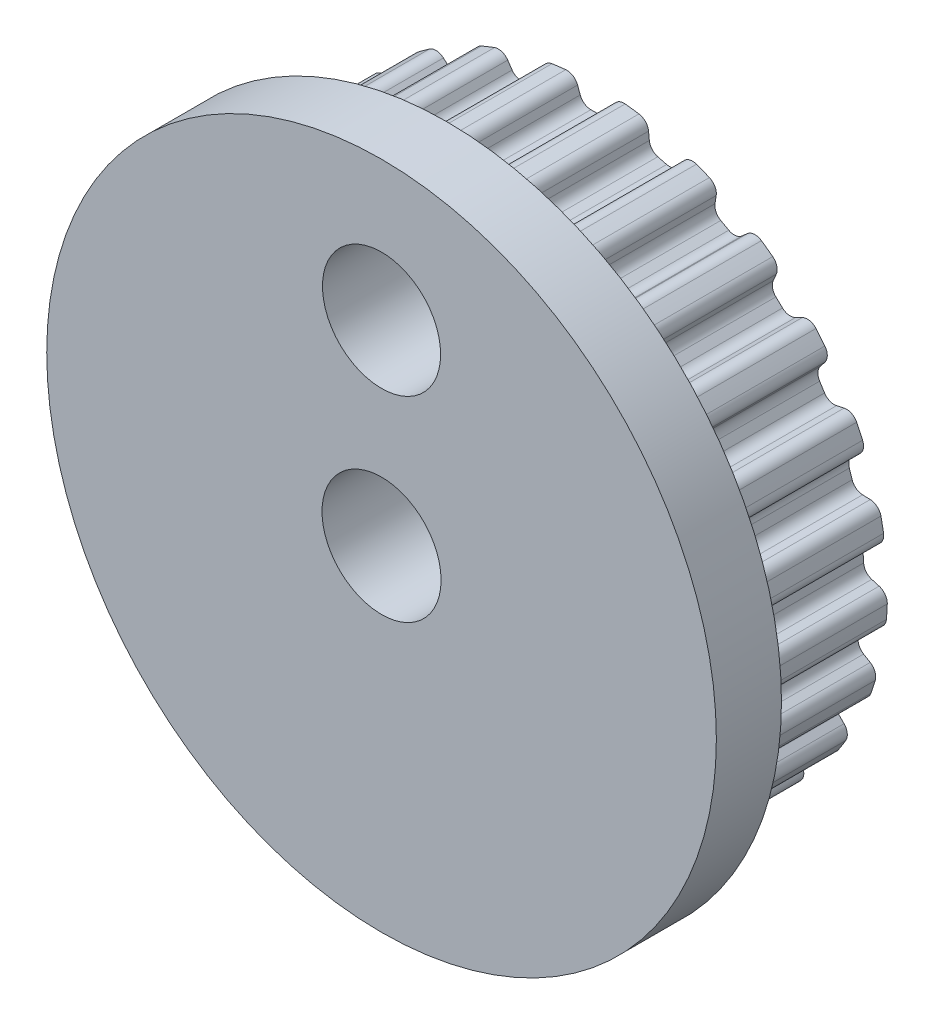
SolidWorks part; units mm, degrees
ref_plane "Front Plane" through (0, 0, 0) normal (0, 0, 1) x (1, 0, 0)
ref_plane "Top Plane" through (0, 0, 0) normal (0, 1, 0) x (1, 0, 0)
ref_plane "Right Plane" through (0, 0, 0) normal (1, 0, 0) x (0, 0, -1)
ref_plane "Plane1" through (0, 0, -5.3) normal (0, 0, -1) x (-1, 0, 0)
sketch "Sketch1" plane through (0, 0, -5.3) normal (0, 0, -1) x (-1, 0, 0)
  line L0 (-2.7705, -6.663) -> (-2.5415, -6.7537)
  line L1 (-2.3491, -7.0456) -> (-2.3549, -7.2528)
  line L2 (-1.4305, -7.4901) -> (-1.3357, -7.3057)
  line L3 (-1.0264, -7.1427) -> (-0.7821, -7.1735)
  line L4 (-0.5231, -7.4084) -> (-0.4772, -7.6106)
  line L5 (0.4772, -7.6106) -> (0.5231, -7.4084)
  line L6 (0.7821, -7.1735) -> (1.0264, -7.1427)
  line L7 (1.3357, -7.3057) -> (1.4305, -7.4901)
  line L8 (2.3549, -7.2528) -> (2.3491, -7.0456)
  line L9 (2.5415, -6.7537) -> (2.7705, -6.663)
  line L10 (3.1106, -6.744) -> (3.2483, -6.8991)
  line L11 (4.0846, -6.4393) -> (4.0274, -6.24)
  line L12 (4.1413, -5.9094) -> (4.3405, -5.7647)
  line L13 (4.6901, -5.7586) -> (4.862, -5.8745)
  line L14 (5.5576, -5.2212) -> (5.4527, -5.0424)
  line L15 (5.4808, -4.6939) -> (5.6377, -4.5041)
  line L16 (5.9748, -4.4113) -> (6.1701, -4.4808)
  line L17 (6.6815, -3.6751) -> (6.5354, -3.528)
  line L18 (6.4759, -3.1834) -> (6.5808, -2.9606)
  line L19 (6.8842, -2.7868) -> (7.0906, -2.8056)
  line L20 (7.3855, -1.898) -> (7.2075, -1.7918)
  line L21 (7.0641, -1.4729) -> (7.1103, -1.231)
  line L22 (7.3609, -0.9872) -> (7.5656, -0.9541)
  line L23 (7.6255, -0.0016) -> (7.4266, 0.0569)
  line L24 (7.2085, 0.3301) -> (7.193, 0.5759)
  line L25 (7.3752, 0.8744) -> (7.5652, 0.9574)
  line L26 (7.3864, 1.8948) -> (7.1792, 1.902)
  line L27 (6.8999, 2.1125) -> (6.8238, 2.3467)
  line L28 (6.9261, 2.681) -> (7.0894, 2.8087)
  line L29 (6.6831, 3.6722) -> (6.4806, 3.6277)
  line L30 (6.1578, 3.762) -> (6.0259, 3.9699)
  line L31 (6.0417, 4.3192) -> (6.1682, 4.4835)
  line L32 (5.5599, 5.2188) -> (5.3748, 5.1254)
  line L33 (5.0288, 5.1752) -> (4.8493, 5.3438)
  line L34 (4.7777, 5.6861) -> (4.8594, 5.8766)
  line L35 (4.0874, 6.4376) -> (3.9314, 6.301)
  line L36 (3.5837, 6.2632) -> (3.368, 6.3819)
  line L37 (3.2136, 6.6956) -> (3.2453, 6.9005)
  line L38 (2.358, 7.2518) -> (2.2409, 7.0807)
  line L39 (1.9136, 6.9577) -> (1.675, 7.0189)
  line L40 (1.4475, 7.2844) -> (1.4273, 7.4908)
  line L41 (0.4805, 7.6104) -> (0.4095, 7.4156)
  line L42 (0.1231, 7.215) -> (-0.1231, 7.215)
  line L43 (-0.4095, 7.4156) -> (-0.4805, 7.6104)
  line L44 (-1.4273, 7.4908) -> (-1.4475, 7.2844)
  line L45 (-1.675, 7.0189) -> (-1.9136, 6.9577)
  line L46 (-2.2409, 7.0807) -> (-2.358, 7.2518)
  line L47 (-3.2453, 6.9005) -> (-3.2136, 6.6956)
  line L48 (-3.368, 6.3819) -> (-3.5837, 6.2632)
  line L49 (-3.9314, 6.301) -> (-4.0874, 6.4376)
  line L50 (-4.8594, 5.8766) -> (-4.7777, 5.6861)
  line L51 (-4.8493, 5.3438) -> (-5.0288, 5.1752)
  line L52 (-5.3748, 5.1254) -> (-5.5599, 5.2188)
  line L53 (-6.1682, 4.4835) -> (-6.0417, 4.3192)
  line L54 (-6.0259, 3.9699) -> (-6.1578, 3.762)
  line L55 (-6.4806, 3.6277) -> (-6.6831, 3.6722)
  line L56 (-7.0894, 2.8087) -> (-6.9261, 2.681)
  line L57 (-6.8238, 2.3467) -> (-6.8999, 2.1125)
  line L58 (-7.1792, 1.902) -> (-7.3864, 1.8948)
  line L59 (-7.5652, 0.9574) -> (-7.3752, 0.8744)
  line L60 (-7.193, 0.5759) -> (-7.2085, 0.3301)
  line L61 (-7.4266, 0.0569) -> (-7.6255, -0.0016)
  line L62 (-7.5656, -0.9541) -> (-7.3609, -0.9872)
  line L63 (-7.1103, -1.231) -> (-7.0641, -1.4729)
  line L64 (-7.2075, -1.7918) -> (-7.3855, -1.898)
  line L65 (-7.0906, -2.8056) -> (-6.8842, -2.7868)
  line L66 (-6.5808, -2.9606) -> (-6.4759, -3.1834)
  line L67 (-6.5354, -3.528) -> (-6.6815, -3.6751)
  line L68 (-6.1701, -4.4808) -> (-5.9748, -4.4113)
  line L69 (-5.6377, -4.5041) -> (-5.4808, -4.6939)
  line L70 (-5.4527, -5.0424) -> (-5.5576, -5.2212)
  line L71 (-4.862, -5.8745) -> (-4.6901, -5.7586)
  line L72 (-4.3405, -5.7647) -> (-4.1413, -5.9094)
  line L73 (-4.0274, -6.24) -> (-4.0846, -6.4393)
  line L74 (-3.2483, -6.8991) -> (-3.1106, -6.744)
  arc A2 (-2.5415, -6.7537) -> (-2.3491, -7.0456) centre (-2.6537, -7.0371) cw
  arc A3 (-2.3549, -7.2528) -> (-2.133, -7.5547) centre (-2.0502, -7.2613) ccw
  arc A4 (-2.133, -7.5547) -> (-1.7703, -7.6478) centre (0, 0) ccw
  arc A5 (-1.7703, -7.6478) -> (-1.4305, -7.4901) centre (-1.7016, -7.3508) ccw
  arc A6 (-1.3357, -7.3057) -> (-1.0264, -7.1427) centre (-1.0646, -7.4451) cw
  arc A7 (-0.7821, -7.1735) -> (-0.5231, -7.4084) centre (-0.8203, -7.4759) cw
  arc A8 (-0.4772, -7.6106) -> (-0.1872, -7.8478) centre (-0.1799, -7.5431) ccw
  arc A9 (-0.1872, -7.8478) -> (0.1872, -7.8478) centre (0, 0) ccw
  arc A10 (0.1872, -7.8478) -> (0.4772, -7.6106) centre (0.1799, -7.5431) ccw
  arc A11 (0.5231, -7.4084) -> (0.7821, -7.1735) centre (0.8203, -7.4759) cw
  arc A12 (1.0264, -7.1427) -> (1.3357, -7.3057) centre (1.0646, -7.4451) cw
  arc A13 (1.4305, -7.4901) -> (1.7703, -7.6478) centre (1.7016, -7.3508) ccw
  arc A14 (1.7703, -7.6478) -> (2.133, -7.5547) centre (0, 0) ccw
  arc A15 (2.133, -7.5547) -> (2.3549, -7.2528) centre (2.0502, -7.2613) ccw
  arc A16 (2.3491, -7.0456) -> (2.5415, -6.7537) centre (2.6537, -7.0371) cw
  arc A17 (2.7705, -6.663) -> (3.1106, -6.744) centre (2.8827, -6.9464) cw
  arc A18 (3.2483, -6.8991) -> (3.6166, -6.9672) centre (3.4762, -6.6967) ccw
  arc A19 (3.6166, -6.9672) -> (3.9447, -6.7869) centre (0, 0) ccw
  arc A20 (3.9447, -6.7869) -> (4.0846, -6.4393) centre (3.7916, -6.5233) ccw
  arc A21 (4.0274, -6.24) -> (4.1413, -5.9094) centre (4.3204, -6.156) cw
  arc A22 (4.3405, -5.7647) -> (4.6901, -5.7586) centre (4.5196, -6.0113) cw
  arc A23 (4.862, -5.8745) -> (5.2357, -5.8489) centre (5.0324, -5.6218) ccw
  arc A24 (5.2357, -5.8489) -> (5.5086, -5.5926) centre (0, 0) ccw
  arc A25 (5.5086, -5.5926) -> (5.5576, -5.2212) centre (5.2947, -5.3755) ccw
  arc A26 (5.4527, -5.0424) -> (5.4808, -4.6939) centre (5.7156, -4.8882) cw
  arc A27 (5.6377, -4.5041) -> (5.9748, -4.4113) centre (5.8726, -4.6984) cw
  arc A28 (6.1701, -4.4808) -> (6.5258, -4.3631) centre (6.2724, -4.1937) ccw
  arc A29 (6.5258, -4.3631) -> (6.7264, -4.047) centre (0, 0) ccw
  arc A30 (6.7264, -4.047) -> (6.6815, -3.6751) centre (6.4652, -3.8898) ccw
  arc A31 (6.5354, -3.528) -> (6.4759, -3.1834) centre (6.7517, -3.3132) cw
  arc A32 (6.5808, -2.9606) -> (6.8842, -2.7868) centre (6.8565, -3.0904) cw
  arc A33 (7.0906, -2.8056) -> (7.4058, -2.6031) centre (7.1183, -2.5021) ccw
  arc A34 (7.4058, -2.6031) -> (7.5215, -2.247) centre (0, 0) ccw
  arc A35 (7.5215, -2.247) -> (7.3855, -1.898) centre (7.2295, -2.1598) ccw
  arc A36 (7.2075, -1.7918) -> (7.0641, -1.4729) centre (7.3635, -1.53) cw
  arc A37 (7.1103, -1.231) -> (7.3609, -0.9872) centre (7.4097, -1.2881) cw
  arc A38 (7.5656, -0.9541) -> (7.8205, -0.6796) centre (7.5169, -0.6532) ccw
  arc A39 (7.8205, -0.6796) -> (7.844, -0.3059) centre (0, 0) ccw
  arc A40 (7.844, -0.3059) -> (7.6255, -0.0016) centre (7.5395, -0.294) ccw
  arc A41 (7.4266, 0.0569) -> (7.2085, 0.3301) centre (7.5127, 0.3493) cw
  arc A42 (7.193, 0.5759) -> (7.3752, 0.8744) centre (7.4972, 0.5951) cw
  arc A43 (7.5652, 0.9574) -> (7.7438, 1.2866) centre (7.4432, 1.2367) ccw
  arc A44 (7.7438, 1.2866) -> (7.6737, 1.6544) centre (0, 0) ccw
  arc A45 (7.6737, 1.6544) -> (7.3864, 1.8948) centre (7.3757, 1.5902) ccw
  arc A46 (7.1792, 1.902) -> (6.8999, 2.1125) centre (7.1898, 2.2066) cw
  arc A47 (6.8238, 2.3467) -> (6.9261, 2.681) centre (7.1137, 2.4408) cw
  arc A48 (7.0894, 2.8087) -> (7.1806, 3.172) centre (6.9018, 3.0489) ccw
  arc A49 (7.1806, 3.172) -> (7.0212, 3.5108) centre (0, 0) ccw
  arc A50 (7.0212, 3.5108) -> (6.6831, 3.6722) centre (6.7485, 3.3745) ccw
  arc A51 (6.4806, 3.6277) -> (6.1578, 3.762) centre (6.4152, 3.9254) cw
  arc A52 (6.0259, 3.9699) -> (6.0417, 4.3192) centre (6.2832, 4.1333) cw
  arc A53 (6.1682, 4.4835) -> (6.1661, 4.8581) centre (5.9267, 4.6695) ccw
  arc A54 (6.1661, 4.8581) -> (5.9275, 5.1466) centre (0, 0) ccw
  arc A55 (5.9275, 5.1466) -> (5.5599, 5.2188) centre (5.6973, 4.9468) ccw
  arc A56 (5.3748, 5.1254) -> (5.0288, 5.1752) centre (5.2374, 5.3974) cw
  arc A57 (4.8493, 5.3438) -> (4.7777, 5.6861) centre (5.0579, 5.566) cw
  arc A58 (4.8594, 5.8766) -> (4.7643, 6.2389) centre (4.5793, 5.9967) ccw
  arc A59 (4.7643, 6.2389) -> (4.4613, 6.459) centre (0, 0) ccw
  arc A60 (4.4613, 6.459) -> (4.0874, 6.4376) centre (4.2881, 6.2082) ccw
  arc A61 (3.9314, 6.301) -> (3.5837, 6.2632) centre (3.7306, 6.5303) cw
  arc A62 (3.368, 6.3819) -> (3.2136, 6.6956) centre (3.5148, 6.649) cw
  arc A63 (3.2453, 6.9005) -> (3.063, 7.2278) centre (2.9441, 6.9471) ccw
  arc A64 (3.063, 7.2278) -> (2.7149, 7.3656) centre (0, 0) ccw
  arc A65 (2.7149, 7.3656) -> (2.358, 7.2518) centre (2.6095, 7.0796) ccw
  arc A66 (2.2409, 7.0807) -> (1.9136, 6.9577) centre (1.9894, 7.2529) cw
  arc A67 (1.675, 7.0189) -> (1.4475, 7.2844) centre (1.7508, 7.3142) cw
  arc A68 (1.4273, 7.4908) -> (1.1693, 7.7624) centre (1.1239, 7.461) ccw
  arc A69 (1.1693, 7.7624) -> (0.7979, 7.8093) centre (0, 0) ccw
  arc A70 (0.7979, 7.8093) -> (0.4805, 7.6104) centre (0.7669, 7.5061) ccw
  arc A71 (0.4095, 7.4156) -> (0.1231, 7.215) centre (0.1231, 7.5198) cw
  arc A72 (-0.1231, 7.215) -> (-0.4095, 7.4156) centre (-0.1231, 7.5198) cw
  arc A73 (-0.4805, 7.6104) -> (-0.7979, 7.8093) centre (-0.7669, 7.5061) ccw
  arc A74 (-0.7979, 7.8093) -> (-1.1693, 7.7624) centre (0, 0) ccw
  arc A75 (-1.1693, 7.7624) -> (-1.4273, 7.4908) centre (-1.1239, 7.461) ccw
  arc A76 (-1.4475, 7.2844) -> (-1.675, 7.0189) centre (-1.7508, 7.3142) cw
  arc A77 (-1.9136, 6.9577) -> (-2.2409, 7.0807) centre (-1.9894, 7.2529) cw
  arc A78 (-2.358, 7.2518) -> (-2.7149, 7.3656) centre (-2.6095, 7.0796) ccw
  arc A79 (-2.7149, 7.3656) -> (-3.063, 7.2278) centre (0, 0) ccw
  arc A80 (-3.063, 7.2278) -> (-3.2453, 6.9005) centre (-2.9441, 6.9471) ccw
  arc A81 (-3.2136, 6.6956) -> (-3.368, 6.3819) centre (-3.5148, 6.649) cw
  arc A82 (-3.5837, 6.2632) -> (-3.9314, 6.301) centre (-3.7306, 6.5303) cw
  arc A83 (-4.0874, 6.4376) -> (-4.4613, 6.459) centre (-4.2881, 6.2082) ccw
  arc A84 (-4.4613, 6.459) -> (-4.7643, 6.2389) centre (0, 0) ccw
  arc A85 (-4.7643, 6.2389) -> (-4.8594, 5.8766) centre (-4.5793, 5.9967) ccw
  arc A86 (-4.7777, 5.6861) -> (-4.8493, 5.3438) centre (-5.0579, 5.566) cw
  arc A87 (-5.0288, 5.1752) -> (-5.3748, 5.1254) centre (-5.2374, 5.3974) cw
  arc A88 (-5.5599, 5.2188) -> (-5.9275, 5.1466) centre (-5.6973, 4.9468) ccw
  arc A89 (-5.9275, 5.1466) -> (-6.1661, 4.8581) centre (0, 0) ccw
  arc A90 (-6.1661, 4.8581) -> (-6.1682, 4.4835) centre (-5.9267, 4.6695) ccw
  arc A91 (-6.0417, 4.3192) -> (-6.0259, 3.9699) centre (-6.2832, 4.1333) cw
  arc A92 (-6.1578, 3.762) -> (-6.4806, 3.6277) centre (-6.4152, 3.9254) cw
  arc A93 (-6.6831, 3.6722) -> (-7.0212, 3.5108) centre (-6.7485, 3.3745) ccw
  arc A94 (-7.0212, 3.5108) -> (-7.1806, 3.172) centre (0, 0) ccw
  arc A95 (-7.1806, 3.172) -> (-7.0894, 2.8087) centre (-6.9018, 3.0489) ccw
  arc A96 (-6.9261, 2.681) -> (-6.8238, 2.3467) centre (-7.1137, 2.4408) cw
  arc A97 (-6.8999, 2.1125) -> (-7.1792, 1.902) centre (-7.1898, 2.2066) cw
  arc A98 (-7.3864, 1.8948) -> (-7.6737, 1.6544) centre (-7.3757, 1.5902) ccw
  arc A99 (-7.6737, 1.6544) -> (-7.7438, 1.2866) centre (0, 0) ccw
  arc A100 (-7.7438, 1.2866) -> (-7.5652, 0.9574) centre (-7.4432, 1.2367) ccw
  arc A101 (-7.3752, 0.8744) -> (-7.193, 0.5759) centre (-7.4972, 0.5951) cw
  arc A102 (-7.2085, 0.3301) -> (-7.4266, 0.0569) centre (-7.5127, 0.3493) cw
  arc A103 (-7.6255, -0.0016) -> (-7.844, -0.3059) centre (-7.5395, -0.294) ccw
  arc A104 (-7.844, -0.3059) -> (-7.8205, -0.6796) centre (0, 0) ccw
  arc A105 (-7.8205, -0.6796) -> (-7.5656, -0.9541) centre (-7.5169, -0.6532) ccw
  arc A106 (-7.3609, -0.9872) -> (-7.1103, -1.231) centre (-7.4097, -1.2881) cw
  arc A107 (-7.0641, -1.4729) -> (-7.2075, -1.7918) centre (-7.3635, -1.53) cw
  arc A108 (-7.3855, -1.898) -> (-7.5215, -2.247) centre (-7.2295, -2.1598) ccw
  arc A109 (-7.5215, -2.247) -> (-7.4058, -2.6031) centre (0, 0) ccw
  arc A110 (-7.4058, -2.6031) -> (-7.0906, -2.8056) centre (-7.1183, -2.5021) ccw
  arc A111 (-6.8842, -2.7868) -> (-6.5808, -2.9606) centre (-6.8565, -3.0904) cw
  arc A112 (-6.4759, -3.1834) -> (-6.5354, -3.528) centre (-6.7517, -3.3132) cw
  arc A113 (-6.6815, -3.6751) -> (-6.7264, -4.047) centre (-6.4652, -3.8898) ccw
  arc A114 (-6.7264, -4.047) -> (-6.5258, -4.3631) centre (0, 0) ccw
  arc A115 (-6.5258, -4.3631) -> (-6.1701, -4.4808) centre (-6.2724, -4.1937) ccw
  arc A116 (-5.9748, -4.4113) -> (-5.6377, -4.5041) centre (-5.8726, -4.6984) cw
  arc A117 (-5.4808, -4.6939) -> (-5.4527, -5.0424) centre (-5.7156, -4.8882) cw
  arc A118 (-5.5576, -5.2212) -> (-5.5086, -5.5926) centre (-5.2947, -5.3755) ccw
  arc A119 (-5.5086, -5.5926) -> (-5.2357, -5.8489) centre (0, 0) ccw
  arc A120 (-5.2357, -5.8489) -> (-4.862, -5.8745) centre (-5.0324, -5.6218) ccw
  arc A121 (-4.6901, -5.7586) -> (-4.3405, -5.7647) centre (-4.5196, -6.0113) cw
  arc A122 (-4.1413, -5.9094) -> (-4.0274, -6.24) centre (-4.3204, -6.156) cw
  arc A123 (-4.0846, -6.4393) -> (-3.9447, -6.7869) centre (-3.7916, -6.5233) ccw
  arc A124 (-3.9447, -6.7869) -> (-3.6166, -6.9672) centre (0, 0) ccw
  arc A125 (-3.6166, -6.9672) -> (-3.2483, -6.8991) centre (-3.4762, -6.6967) ccw
  arc A126 (-3.1106, -6.744) -> (-2.7705, -6.663) centre (-2.8827, -6.9464) cw
extrude "Boss-Extrude1" add sketch "Sketch1" against normal blind 4
sketch "Sketch2" plane through (0, 0, -1.3) normal (0, 0, 1) x (1, 0, 0)
  circle A0 centre (0, 0) radius 9
extrude "Boss-Extrude2" add sketch "Sketch2" along normal blind 1.75
sketch "Sketch3" plane through (0, 0, 0.45) normal (0, 0, 1) x (1, 0, 0)
  circle A1 centre (0, 0) radius 1.6
  point P5 (0, 0)
sketch "Sketch4" plane through (0, 0, -5.3) normal (0, 0, -1) x (-1, 0, 0)
  line L1 (-2.25, -2.25) -> (2.25, -2.25)
  line L2 (-2.25, -2.25) -> (-2.25, 2.25)
  line L3 (-2.25, 2.25) -> (2.25, 2.25)
  line L4 (2.25, -2.25) -> (2.25, 2.25)
  line L5 (-2.25, -2.25) -> (2.25, 2.25) construction
  line L6 (-2.25, 2.25) -> (2.25, -2.25) construction
  point P0 (0, 0)
  dimension "D1" = 4.5
  dimension "D2" = 4.5
extrude "Boss-Extrude3" add sketch "Sketch4" along normal blind 1.75
extrude "Cut-Extrude2" cut sketch "Sketch3" against normal through all
sketch "Sketch5" plane through (0, 0, 0.45) normal (0, 0, 1) x (1, 0, 0)
  circle A0 centre (0, 5.25) radius 1.5875
extrude "Cut-Extrude3" cut sketch "Sketch5" against normal through all
